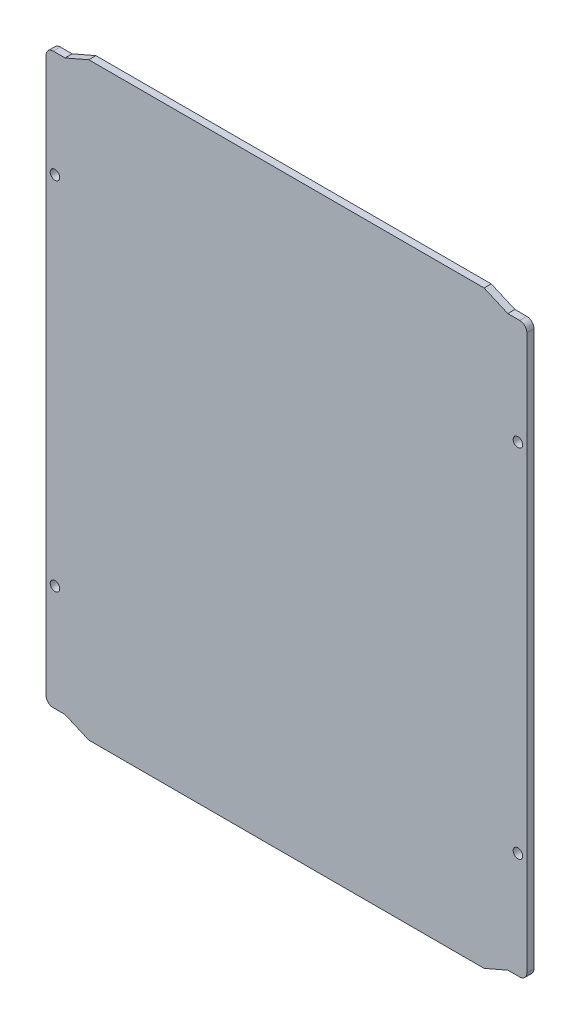
SolidWorks part; units mm, degrees
material "Acrylic (Medium-high impact)"
ref_plane "Front Plane" through (0, 0, 0) normal (0, 0, 1) x (1, 0, 0)
ref_plane "Top Plane" through (0, 0, 0) normal (0, 1, 0) x (1, 0, 0)
ref_plane "Right Plane" through (0, 0, 0) normal (1, 0, 0) x (0, 0, -1)
sketch "Sketch1" plane through (0, 0, 0) normal (0, 0, 1) x (1, 0, 0)
  line L0 (0, 7.34) -> (0, 240.84)
  line L1 (3, 243.84) -> (8, 243.84)
  line L2 (8, 243.84) -> (18, 248.18)
  line L3 (18, 248.18) -> (184.5, 248.18)
  line L4 (184.5, 248.18) -> (194.5, 243.84)
  line L5 (194.5, 243.84) -> (199.5, 243.84)
  line L6 (202.5, 240.84) -> (202.5, 7.34)
  line L7 (199.5, 4.34) -> (194.5, 4.34)
  line L8 (194.5, 4.34) -> (184.5, 0)
  line L9 (184.5, 0) -> (18, 0)
  line L10 (18, 0) -> (8, 4.34)
  line L11 (8, 4.34) -> (3, 4.34)
  arc A0 (0, 240.84) -> (3, 243.84) centre (3, 240.84) cw
  arc A1 (199.5, 243.84) -> (202.5, 240.84) centre (199.5, 240.84) cw
  arc A2 (202.5, 7.34) -> (199.5, 4.34) centre (199.5, 7.34) cw
  arc A3 (3, 4.34) -> (0, 7.34) centre (3, 7.34) cw
  dimension "D2" = 3
  dimension "D1" = 202.5
  dimension "D3" = 8
  dimension "D4" = 4.34
  dimension "D5" = 10
  dimension "D6" = 248.18
extrude "Boss-Extrude1" add sketch "Sketch1" along normal blind 3
hole_wizard "Ø4.0mm Dowel Hole1" positions "Sketch2" profile "Sketch3" hole size "Ø4.0" standard "ANSI Metric" end condition through all
sketch "Sketch2" plane through (0, 0, 3) normal (0, 0, 1) x (1, 0, 0)
  line L0 (3.75, 199.09) -> (3.75, 49.09) construction
  line L4 (0, 240.84) -> (0, 7.34) construction
  line L6 (202.5, 7.34) -> (202.5, 240.84) construction
  point P2 (3.75, 199.09)
  point P4 (3.75, 49.09)
  point P10 (198.75, 49.09)
  point P12 (198.75, 199.09)
  point P37 (3.75, 124.09)
  point P39 (0, 124.09)
  dimension "D1" = 3.75
  dimension "D2" = 3.75
  dimension "D3" = 150
sketch "Sketch3" plane through (3.75, 199.09, 3) normal (1, 0, 0) x (0, -1, 0)
  line L0 (0, 0) -> (0, 3)
  line L1 (0, 3) -> (2, 3)
  line L2 (2, 3) -> (2, 0)
  line L5 (2, 0) -> (0, 0)
  line L11 (0, -6.35) -> (0, 107.95) construction
  dimension "Thru Hole Dia." = 4
  dimension "Thru Hole Depth" = 3
hole_wizard "Ø4.0mm Dowel Hole2" [suppressed] positions "Sketch4" profile "Sketch5" hole size "Ø4.0" standard "ANSI Metric"
sketch "Sketch4" plane through (0, 0, 3) normal (0, 0, 1) x (1, 0, 0)
  line L0 (0, 240.84) -> (0, 7.34) construction
  line L1 (18, 0) -> (232.5, 0) construction
  point P0 (35.77, 49.9)
  point P2 (167.85, 49.9)
  point P4 (167.85, 207.38)
  point P6 (12.91, 207.38)
  dimension "D1" = 35.77
  dimension "D2" = 49.9
  dimension "D3" = 132.08
  dimension "D4" = 157.48
  dimension "D5" = 154.94
sketch "Sketch5" plane through (35.77, 49.9, 3) normal (1, 0, 0) x (0, -1, 0)
  line L0 (0, 0) -> (0, 3)
  line L1 (0, 3) -> (2, 3)
  line L2 (2, 3) -> (2, 0)
  line L5 (2, 0) -> (0, 0)
  line L11 (0, -6.35) -> (0, 107.95) construction
  dimension "Thru Hole Dia." = 4
  dimension "Thru Hole Depth" = 3
sketch "Sketch6" [suppressed] plane through (0, 0, 0) normal (0, 0, -1) x (-1, 0, 0)
  line L0 (-184.5, 248.18) -> (-18, 248.18) construction
  line L1 (-17.5, 228.18) -> (-185, 228.18) construction
  line L2 (-17.5, 228.18) -> (-17.5, 45) construction
  line L3 (-17.5, 45) -> (-185, 45) construction
  line L4 (-185, 228.18) -> (-185, 45) construction
  line L5 (-202.5, 7.34) -> (-202.5, 240.84) construction
  line L6 (-18, 0) -> (-184.5, 0) construction
  line L7 (-174.0303, 223.43) -> (-182.2576, 218.68) construction
  line L8 (-174.0303, 223.43) -> (-176.7728, 228.18)
  line L9 (-176.7728, 228.18) -> (-182.2576, 228.18)
  line L10 (-182.2576, 228.18) -> (-185, 223.43)
  line L11 (-185, 223.43) -> (-182.2576, 218.68)
  line L12 (-182.2576, 218.68) -> (-176.7728, 218.68)
  line L13 (-176.7728, 218.68) -> (-174.0303, 223.43)
  circle A0 centre (-179.5152, 223.43) radius 4.75 construction
  point P6 (-101.25, 248.18)
  point P21 (-101.25, 228.18)
  dimension "D1" = 17.5
  dimension "D2" = 20
  dimension "D3" = 45
  dimension "D4" = 9.5
extrude "Cut-Extrude1" [suppressed] cut sketch "Sketch6" against normal up to next
fillet "Fillet1" [suppressed] radius 3
pattern_linear "LPattern1" [suppressed] count 18 spacing 13 along (0, -1, 0) count 9 spacing 13 along (0.866, -0.5, 0)
sketch "Sketch7" [suppressed] plane through (0, 0, 3) normal (0, 0, 1) x (1, 0, 0)
  line L0 (199.5, 243.84) -> (214, 243.84)
  line L1 (214, 243.84) -> (214, 205.09)
  line L2 (214, 205.09) -> (202.5, 205.09)
  line L3 (202.5, 7.34) -> (202.5, 240.84) construction
  line L4 (202.5, 205.09) -> (202.5, 240.84)
  arc A3 (202.5, 240.84) -> (199.5, 243.84) centre (199.5, 240.84) ccw
  dimension "D3" = 38.75
  dimension "D5" = 11.5
extrude "Boss-Extrude2" [suppressed] add sketch "Sketch7" against normal up to surface (3 mm away)
fillet "Fillet3" [suppressed] radius 4.75
fillet "Fillet2" [suppressed] radius 7.5
sketch "Sketch8" [suppressed] plane through (0, 0, 3) normal (0, 0, 1) x (1, 0, 0)
  circle A0 centre (198.75, 199.09) radius 2 construction
  point P0 (77.75, 190.68)
  point P2 (77.75, 125.68)
  dimension "D1" = 121
  dimension "D2" = 8.41
  dimension "D3" = 65
hole_wizard "Ø4.0mm Dowel Hole4" [suppressed] positions "Sketch10" profile "Sketch11" hole size "Ø4.0" standard "ANSI Metric"
sketch "Sketch10" plane through (0, 0, 3) normal (0, 0, 1) x (1, 0, 0)
  point P0 (77.75, 190.68)
  point P3 (77.75, 125.68)
sketch "Sketch11" plane through (77.75, 190.68, 3) normal (1, 0, 0) x (0, -1, 0)
  line L0 (0, 0) -> (0, 3)
  line L1 (0, 3) -> (2, 3)
  line L2 (2, 3) -> (2, 0.025)
  line L3 (2, 0.025) -> (2.025, 0)
  line L5 (2.025, 0) -> (0, 0)
  line L6 (-2, 0.025) -> (-2.025, 0) construction
  line L11 (0, -6.35) -> (0, 107.95) construction
  dimension "Thru Hole Dia." = 4
  dimension "Thru Hole Depth" = 3
  dimension "Near C'Sink Dia." = 4.05
  dimension "Near C'Sink Angle" = 90
equation "\"beamDepth\"= 187mm"
equation "\"D1@Sketch1\"=15.5 + \"beamDepth\""
